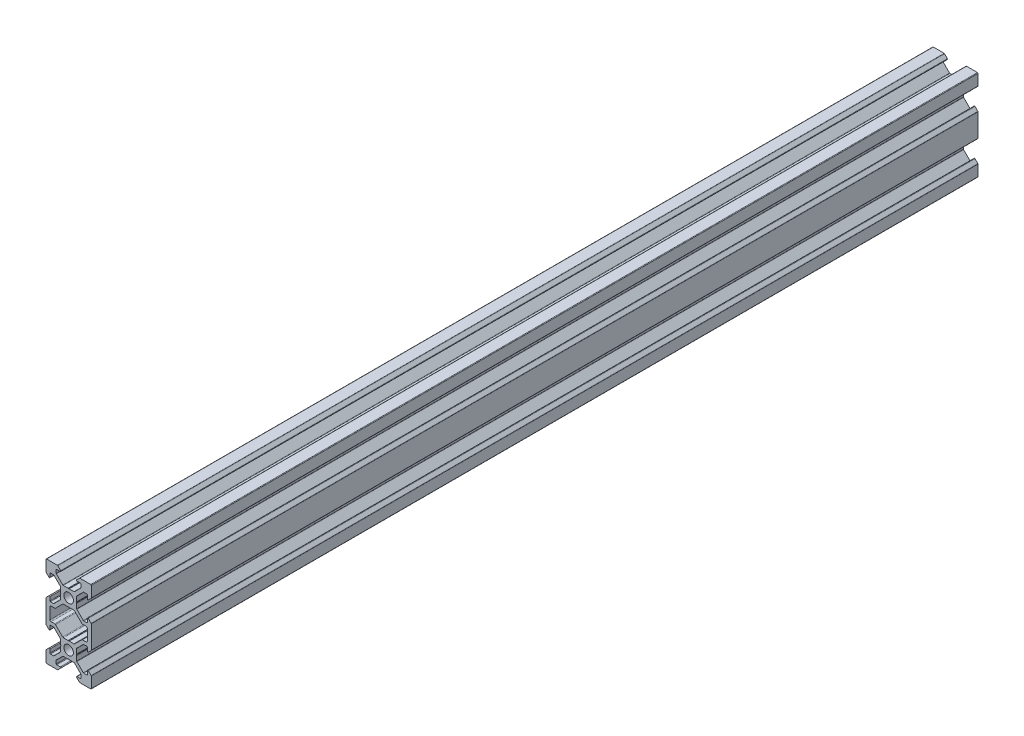
SolidWorks part; units mm, degrees
ref_plane "Front Plane" through (0, 0, 0) normal (0, 0, 1) x (1, 0, 0)
ref_plane "Top Plane" through (0, 0, 0) normal (0, 1, 0) x (1, 0, 0)
ref_plane "Right Plane" through (0, 0, 0) normal (1, 0, 0) x (0, 0, -1)
sketch "Sketch1" plane through (0, 0, 0) normal (0, 0, 1) x (1, 0, 0)
  line L0 (3.5607, 3.5607) -> (10.6317, 10.6317) construction
  line L1 (2.5, -3.5607) -> (-2.5, -3.5607)
  line L2 (3.5607, -2.5) -> (3.5607, 2.5)
  line L3 (2.5, 3.5607) -> (-2.5, 3.5607)
  line L4 (-3.5607, -2.5) -> (-3.5607, 2.5)
  line L5 (3.5607, -3.5607) -> (-3.5607, 3.5607) construction
  line L6 (3.5607, 3.5607) -> (-3.5607, -3.5607) construction
  line L7 (2.5, 3.5607) -> (5.5, 6.5607)
  line L8 (5.5, 6.5607) -> (5.5, 8.2521)
  line L9 (5.5, 8.2521) -> (3.1, 8.2521)
  line L10 (3.1, 8.2521) -> (4.8479, 10)
  line L11 (4.8479, 10) -> (10, 10)
  line L12 (3.5607, 2.5) -> (6.5607, 5.5)
  line L13 (6.5607, 5.5) -> (8.2521, 5.5)
  line L14 (8.2521, 5.5) -> (8.2521, 3.1)
  line L15 (8.2521, 3.1) -> (10, 4.8479)
  line L16 (10, 4.8479) -> (10, 10)
  line L17 (0, -55) -> (0, 55) construction
  line L18 (-3.5607, 3.5607) -> (-10.6317, 10.6317) construction
  line L19 (-10, 4.8479) -> (-10, 10)
  line L20 (-8.2521, 3.1) -> (-10, 4.8479)
  line L21 (-8.2521, 5.5) -> (-8.2521, 3.1)
  line L22 (-6.5607, 5.5) -> (-8.2521, 5.5)
  line L23 (-3.5607, 2.5) -> (-6.5607, 5.5)
  line L24 (-4.8479, 10) -> (-10, 10)
  line L25 (-3.1, 8.2521) -> (-4.8479, 10)
  line L26 (-5.5, 8.2521) -> (-3.1, 8.2521)
  line L27 (-5.5, 6.5607) -> (-5.5, 8.2521)
  line L28 (-2.5, 3.5607) -> (-5.5, 6.5607)
  line L29 (-8.2521, -7) -> (-5.9393, -7)
  line L30 (55, 0) -> (-55, 0) construction
  line L31 (-3.5607, -3.5607) -> (-10.6317, -10.6317) construction
  line L32 (3.5607, -3.5607) -> (10.6317, -10.6317) construction
  line L33 (-2.5, -3.5607) -> (-5.5, -6.5607)
  line L34 (-5.5, -6.5607) -> (-5.9393, -7)
  line L35 (5.5, -6.5607) -> (5.9393, -7)
  line L36 (8.2521, -7) -> (5.9393, -7)
  line L37 (-12.2633, -10) -> (14.5346, -10) construction
  line L38 (-3.5607, -2.5) -> (-6.5607, -5.5)
  line L39 (-6.5607, -5.5) -> (-8.2521, -5.5)
  line L40 (-8.2521, -5.5) -> (-8.2521, -3.1)
  line L41 (-8.2521, -3.1) -> (-10, -4.8479)
  line L42 (-10, -4.8479) -> (-10, -7)
  line L43 (10, -4.8479) -> (10, -7)
  line L44 (8.2521, -3.1) -> (10, -4.8479)
  line L45 (8.2521, -5.5) -> (8.2521, -3.1)
  line L46 (6.5607, -5.5) -> (8.2521, -5.5)
  line L47 (3.5607, -2.5) -> (6.5607, -5.5)
  line L48 (-3.5607, -23.5607) -> (-10.6317, -30.6317) construction
  line L49 (3.5607, -23.5607) -> (-3.5607, -16.4393) construction
  line L50 (3.5607, -16.4393) -> (-3.5607, -23.5607) construction
  line L51 (3.5607, -23.5607) -> (10.6317, -30.6317) construction
  line L52 (2.5, -3.5607) -> (5.5, -6.5607)
  line L53 (2.5, -16.4393) -> (5.5, -13.4393)
  line L54 (3.5607, -17.5) -> (6.5607, -14.5)
  line L55 (6.5607, -14.5) -> (8.2521, -14.5)
  line L56 (8.2521, -14.5) -> (8.2521, -16.9)
  line L57 (8.2521, -16.9) -> (10, -15.1521)
  line L58 (10, -15.1521) -> (10, -13)
  line L59 (-10, -15.1521) -> (-10, -13)
  line L60 (-8.2521, -16.9) -> (-10, -15.1521)
  line L61 (-8.2521, -14.5) -> (-8.2521, -16.9)
  line L62 (-6.5607, -14.5) -> (-8.2521, -14.5)
  line L63 (-3.5607, -17.5) -> (-6.5607, -14.5)
  line L64 (8.2521, -13) -> (5.9393, -13)
  line L65 (5.5, -13.4393) -> (5.9393, -13)
  line L66 (-5.5, -13.4393) -> (-5.9393, -13)
  line L67 (-2.5, -16.4393) -> (-5.5, -13.4393)
  line L68 (-8.2521, -13) -> (-5.9393, -13)
  line L69 (-2.5, -23.5607) -> (-5.5, -26.5607)
  line L70 (-5.5, -26.5607) -> (-5.5, -28.2521)
  line L71 (-5.5, -28.2521) -> (-3.1, -28.2521)
  line L72 (-3.1, -28.2521) -> (-4.8479, -30)
  line L73 (-4.8479, -30) -> (-10, -30)
  line L74 (-3.5607, -22.5) -> (-6.5607, -25.5)
  line L75 (-6.5607, -25.5) -> (-8.2521, -25.5)
  line L76 (-8.2521, -25.5) -> (-8.2521, -23.1)
  line L77 (-8.2521, -23.1) -> (-10, -24.8479)
  line L78 (-10, -24.8479) -> (-10, -30)
  line L79 (10, -24.8479) -> (10, -30)
  line L80 (8.2521, -23.1) -> (10, -24.8479)
  line L81 (8.2521, -25.5) -> (8.2521, -23.1)
  line L82 (6.5607, -25.5) -> (8.2521, -25.5)
  line L83 (3.5607, -22.5) -> (6.5607, -25.5)
  line L84 (4.8479, -30) -> (10, -30)
  line L85 (3.1, -28.2521) -> (4.8479, -30)
  line L86 (5.5, -28.2521) -> (3.1, -28.2521)
  line L87 (5.5, -26.5607) -> (5.5, -28.2521)
  line L88 (2.5, -23.5607) -> (5.5, -26.5607)
  line L89 (-3.5607, -17.5) -> (-3.5607, -22.5)
  line L90 (2.5, -23.5607) -> (-2.5, -23.5607)
  line L91 (3.5607, -17.5) -> (3.5607, -22.5)
  line L92 (2.5, -16.4393) -> (-2.5, -16.4393)
  line L93 (-10, -7) -> (-10, -13)
  line L94 (-8.2521, -13) -> (-8.2521, -7)
  line L95 (8.2521, -13) -> (8.2521, -7)
  line L96 (10, -7) -> (10, -13)
  circle A0 centre (0, 0) radius 2.1
  circle A1 centre (0, -20) radius 2.1
  point P0 (0, 0)
  point P102 (0, -20)
  dimension "D10" = 4.2
  dimension "D11" = 4.2
  dimension "D1" = 1.5
  dimension "D2" = 10
  dimension "D3" = 20
  dimension "D4" = 6.2
  dimension "D5" = 11
  dimension "D6" = 45
  dimension "D7" = 1.5
  dimension "D8" = 10
  dimension "D9" = 5
extrude "Boss-Extrude1" add sketch "Sketch1" along normal blind 391.83
fillet "Fillet1" radius 0.25 64 edges at (5.5, 6.5607, 195.915) (5.5, 8.2521, 195.915) (3.1, 8.2521, 195.915) (4.8479, 10, 195.915) (10, 10, 195.915) (10, 4.8479, 195.915) (8.2521, 3.1, 195.915) (8.2521, 5.5, 195.915) (6.5607, 5.5, 195.915) (3.5607, 2.5, 195.915) (3.5607, -2.5, 195.915) (6.5607, -5.5, 195.915) (8.2521, -5.5, 195.915) (8.2521, -3.1, 195.915) (10, -4.8479, 195.915) (10, -15.1521, 195.915) (8.2521, -16.9, 195.915) (8.2521, -14.5, 195.915) (6.5607, -14.5, 195.915) (3.5607, -17.5, 195.915) (3.5607, -22.5, 195.915) (6.5607, -25.5, 195.915) (8.2521, -25.5, 195.915) (8.2521, -23.1, 195.915) (10, -24.8479, 195.915) (10, -30, 195.915) (4.8479, -30, 195.915) (3.1, -28.2521, 195.915) (5.5, -28.2521, 195.915) (5.5, -26.5607, 195.915) (2.5, -23.5607, 195.915) (-2.5, -23.5607, 195.915) (-5.5, -26.5607, 195.915) (-5.5, -28.2521, 195.915) (-3.1, -28.2521, 195.915) (-4.8479, -30, 195.915) (-10, -30, 195.915) (-10, -24.8479, 195.915) (-8.2521, -23.1, 195.915) (-8.2521, -25.5, 195.915) (-6.5607, -25.5, 195.915) (-3.5607, -22.5, 195.915) (-3.5607, -17.5, 195.915) (-6.5607, -14.5, 195.915) (-8.2521, -14.5, 195.915) (-8.2521, -16.9, 195.915) (-10, -15.1521, 195.915) (-10, -4.8479, 195.915) (-8.2521, -3.1, 195.915) (-8.2521, -5.5, 195.915) (-6.5607, -5.5, 195.915) (-3.5607, -2.5, 195.915) (-3.5607, 2.5, 195.915) (-6.5607, 5.5, 195.915) (-8.2521, 5.5, 195.915) (-8.2521, 3.1, 195.915) (-10, 4.8479, 195.915) (-10, 10, 195.915) (-4.8479, 10, 195.915) (-5.5, 8.2521, 195.915) (-5.5, 6.5607, 195.915) (-2.5, 3.5607, 195.915) (2.5, 3.5607, 195.915) (-3.1, 8.2521, 195.915)
fillet "Fillet2" radius 0.5 12 edges at (-5.9393, -7, 195.915) (-8.2521, -7, 195.915) (-8.2521, -13, 195.915) (-5.9393, -13, 195.915) (-2.5, -16.4393, 195.915) (2.5, -16.4393, 195.915) (8.2521, -7, 195.915) (5.9393, -7, 195.915) (2.5, -3.5607, 195.915) (-2.5, -3.5607, 195.915) (5.9393, -13, 195.915) (8.2521, -13, 195.915)
sketch "Sketch2" plane through (0, 0, 391.83) normal (0, 0, 1) x (1, 0, 0)
  line L4 (0, 3.5607) -> (0, 3.1447) construction
  line L5 (2.3964, 3.5607) -> (-2.3964, 3.5607) construction
  line L6 (0, 3.399) -> (-0.2423, 3.5607)
  line L7 (0, 3.399) -> (0.2423, 3.5607)
  line L8 (-0.2423, 3.5607) -> (0.2423, 3.5607)
  line L9 (55, 0) -> (-55, 0) construction
  line L10 (0, -3.5607) -> (0, -3.1447) construction
  line L11 (0, -3.399) -> (0.2423, -3.5607)
  line L12 (0, -3.399) -> (-0.2423, -3.5607)
  line L13 (-0.2423, -3.5607) -> (0.2423, -3.5607)
  line L14 (0, 0) -> (-4.0856, 4.0856) construction
  line L15 (-8.2521, -10) -> (4.1581, -10) construction
  line L16 (-8.2521, -7.5) -> (-8.2521, -12.5) construction
  line L17 (3.5607, 0) -> (3.1447, 0) construction
  line L18 (3.5607, 0.2423) -> (3.5607, -0.2423)
  line L19 (3.399, 0) -> (3.5607, 0.2423)
  line L20 (3.399, 0) -> (3.5607, -0.2423)
  line L21 (-3.5607, 0) -> (-3.1447, 0) construction
  line L22 (-3.5607, 0.2423) -> (-3.5607, -0.2423)
  line L23 (-3.399, 0) -> (-3.5607, -0.2423)
  line L24 (-3.399, 0) -> (-3.5607, 0.2423)
  line L25 (-3.5607, -20) -> (-3.1447, -20) construction
  line L26 (3.5607, -20) -> (3.1447, -20) construction
  line L27 (0, -20) -> (-4.0856, -24.0856) construction
  line L28 (0, -16.4393) -> (0, -16.8553) construction
  line L29 (0, -23.5607) -> (0, -23.1447) construction
  line L30 (-3.399, -20) -> (-3.5607, -20.2423)
  line L31 (-3.399, -20) -> (-3.5607, -19.7577)
  line L32 (-3.5607, -20.2423) -> (-3.5607, -19.7577)
  line L33 (3.399, -20) -> (3.5607, -19.7577)
  line L34 (3.399, -20) -> (3.5607, -20.2423)
  line L35 (3.5607, -20.2423) -> (3.5607, -19.7577)
  line L36 (-0.2423, -16.4393) -> (0.2423, -16.4393)
  line L37 (0, -16.601) -> (-0.2423, -16.4393)
  line L38 (0, -16.601) -> (0.2423, -16.4393)
  line L39 (-0.2423, -23.5607) -> (0.2423, -23.5607)
  line L40 (0, -23.399) -> (0.2423, -23.5607)
  line L41 (0, -23.399) -> (-0.2423, -23.5607)
extrude "Cut-Extrude1" cut sketch "Sketch2" against normal through all
